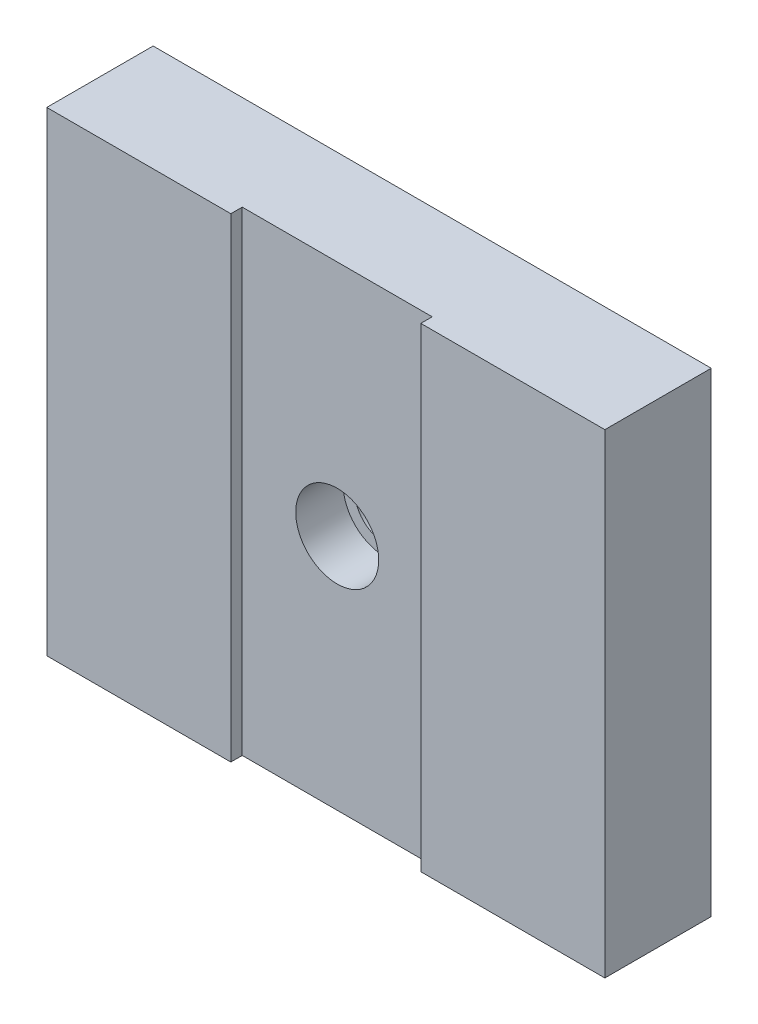
SolidWorks part; units mm, degrees
material "6061-T6 Al"
ref_plane "Front Plane" through (0, 0, 0) normal (0, 0, 1) x (1, 0, 0)
ref_plane "Top Plane" through (0, 0, 0) normal (0, 1, 0) x (1, 0, 0)
ref_plane "Right Plane" through (0, 0, 0) normal (1, 0, 0) x (0, 0, -1)
sketch "Sketch1" plane through (0, 0, 0) normal (0, 0, 1) x (1, 0, 0)
  line L1 (0, 0) -> (74.6252, 0)
  line L2 (0, 0) -> (0, 63.5)
  line L3 (0, 63.5) -> (74.6252, 63.5)
  line L4 (74.6252, 0) -> (74.6252, 63.5)
  dimension "D1" = 63.5
  dimension "D2" = 74.6252
extrude "Boss-Extrude1" add sketch "Sketch1" along normal blind 14.224
hole_wizard "CBORE for 1/4 Socket Head Cap Screw1" positions "Sketch6" profile "Sketch5" counterbore size "1/4" standard "Ansi Inch" end condition through all
sketch "Sketch6" plane through (0, 0, 14.224) normal (0, 0, 1) x (1, 0, 0)
  line L5 (0, 0) -> (74.6252, 63.5) construction
  point P0 (37.3126, 31.75)
sketch "Sketch5" plane through (37.3126, 31.75, 14.224) normal (1, 0, 0) x (0, -1, 0)
  line L0 (0, 0) -> (0, 14.224)
  line L1 (0, 14.224) -> (4.0132, 14.224)
  line L3 (4.0132, 14.224) -> (4.0132, 7.874)
  line L4 (4.0132, 7.874) -> (5.5499, 7.874)
  line L5 (5.5499, 7.874) -> (5.5499, 0)
  line L7 (5.5499, 0) -> (0, 0)
  line L11 (0, -6.35) -> (0, 107.95) construction
  dimension "Thru Hole Dia." = 8.0264
  dimension "Thru Hole Depth" = 14.224
  dimension "C'Bore Dia." = 11.0998
  dimension "C'Bore Depth" = 7.874
sketch "Sketch9" plane through (0, 0, 14.224) normal (0, 0, 1) x (1, 0, 0)
  line L0 (37.3126, 31.75) -> (37.3126, 0) construction
  line L1 (50.0126, 0) -> (24.6126, 0)
  line L2 (50.0126, 0) -> (50.0126, 63.5)
  line L3 (50.0126, 63.5) -> (24.6126, 63.5)
  line L4 (24.6126, 0) -> (24.6126, 63.5)
  line L5 (37.3126, 31.75) -> (37.3126, 63.5) construction
  line L6 (74.6252, 63.5) -> (0, 63.5) construction
  line L7 (0, 0) -> (74.6252, 0) construction
  dimension "D1" = 25.4
extrude "Cut-Extrude1" cut sketch "Sketch9" against normal blind 1.524
sketch "Sketch10" plane through (0, 0, 0) normal (0, 0, -1) x (-1, 0, 0)
  circle A0 centre (-37.3126, 31.75) radius 11.1125
  dimension "D1" = 22.225
extrude "Cut-Extrude2" cut sketch "Sketch10" against normal blind 1.397
